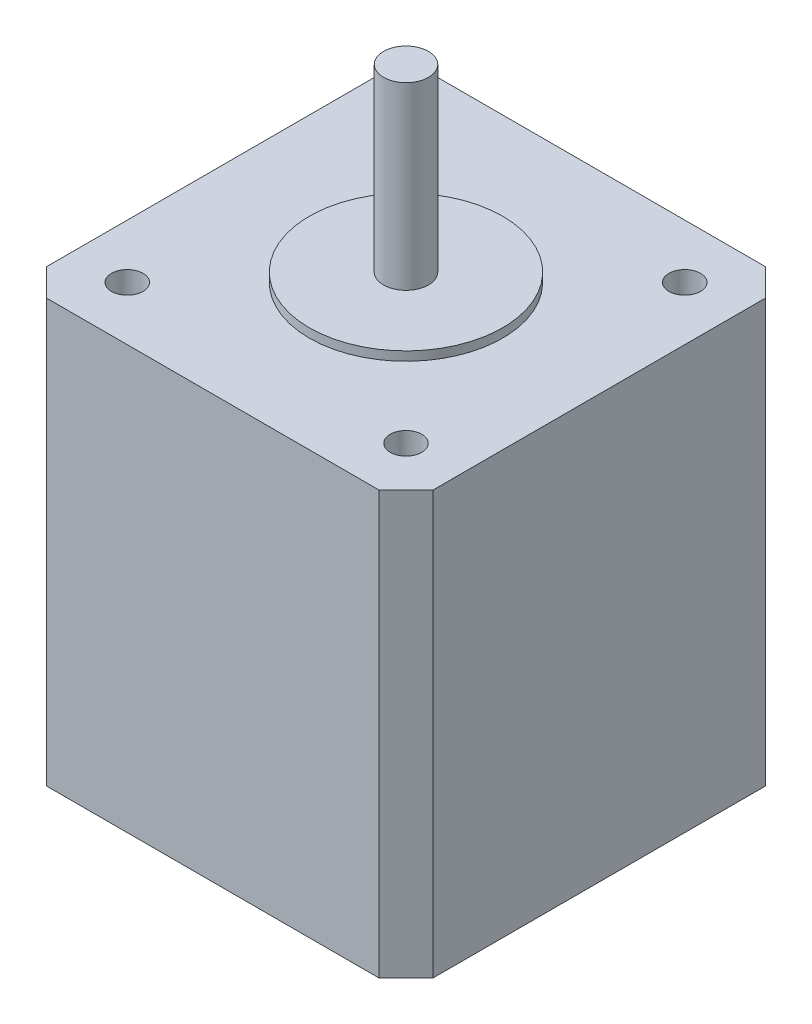
SolidWorks part; units mm, degrees
ref_plane "Front Plane" through (0, 0, 0) normal (0, 0, 1) x (1, 0, 0)
ref_plane "Top Plane" through (0, 0, 0) normal (0, 1, 0) x (1, 0, 0)
ref_plane "Right Plane" through (0, 0, 0) normal (1, 0, 0) x (0, 0, -1)
sketch "Sketch1" plane through (0, 0, 0) normal (0, 1, 0) x (1, 0, 0)
  line L1 (0, 0) -> (43, 0)
  line L2 (0, 0) -> (0, 43)
  line L3 (0, 43) -> (43, 43)
  line L4 (43, 0) -> (43, 43)
  dimension "D1" = 43
  dimension "D2" = 43
extrude "Boss-Extrude1" add sketch "Sketch1" along normal blind 47
sketch "Sketch2" plane through (0, 47, 0) normal (0, 1, 0) x (1, 0, 0)
  line L0 (0, 43) -> (43, 0) construction
  circle A0 centre (21.5, 21.5) radius 10.75
  dimension "D1" = 21.5
extrude "Boss-Extrude2" add sketch "Sketch2" along normal blind 1
sketch "Sketch3" plane through (0, 48, 0) normal (0, 1, 0) x (1, 0, 0)
  circle A0 centre (21.5, 21.5) radius 2.5
  circle A1 centre (21.5, 21.5) radius 10.75 construction
  dimension "D1" = 5
extrude "Boss-Extrude3" add sketch "Sketch3" along normal blind 20
chamfer "Chamfer1" distance 3 angle 45 3 edges at (0, 23.5, -43) (43, 23.5, -43) (0, 23.5, 0)
sketch "Sketch4" plane through (0, 47, 0) normal (0, 1, 0) x (1, 0, 0)
  line L1 (6, 6) -> (37, 6) construction
  line L2 (6, 6) -> (6, 37) construction
  line L3 (6, 37) -> (37, 37) construction
  line L4 (37, 6) -> (37, 37) construction
  line L5 (0, 0) -> (41.5, 41.5) construction
  line L6 (43, 40) -> (40, 43) construction
  line L7 (1.5, 41.5) -> (41.5, 1.5) construction
  line L8 (3, 43) -> (0, 40) construction
  line L9 (40, 0) -> (43, 3) construction
  circle A2 centre (6, 37) radius 1.75
  circle A3 centre (6, 6) radius 1.75
  circle A4 centre (37, 6) radius 1.75
  circle A5 centre (37, 37) radius 1.75
  dimension "D1" = 31
  dimension "D3" = 3.5
  dimension "D4" = 3.5
  dimension "D5" = 3.5
  dimension "D6" = 3.5
  dimension "D2" = 31
extrude "Cut-Extrude2" cut sketch "Sketch4" against normal blind 10
